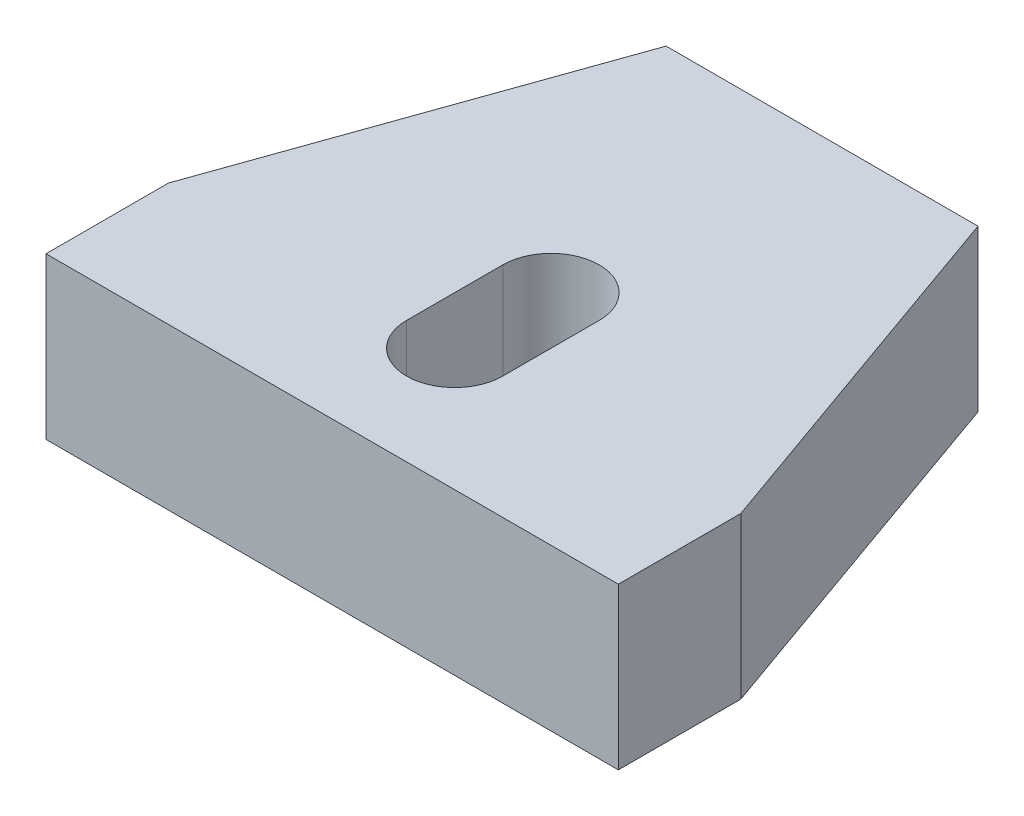
SolidWorks part; units mm, degrees
ref_plane "Front Plane" through (0, 0, 0) normal (0, 0, 1) x (1, 0, 0)
ref_plane "Top Plane" through (0, 0, 0) normal (0, 1, 0) x (1, 0, 0)
ref_plane "Right Plane" through (0, 0, 0) normal (1, 0, 0) x (0, 0, -1)
sketch "Sketch1" plane through (0, 0, 0) normal (0, 1, 0) x (1, 0, 0)
  line L0 (-8.9027, 0) -> (8.9027, 0)
  line L1 (8.9027, 0) -> (8.9027, 3.81)
  line L2 (-8.9027, 0) -> (-8.9027, 3.81)
  line L3 (-4.8514, 15.24) -> (4.8514, 15.24)
  line L4 (8.9027, 3.81) -> (4.8514, 15.24)
  line L5 (-4.8514, 15.24) -> (-8.9027, 3.81)
  line L6 (0, 15.24) -> (0, 0) construction
  line L7 (0, 3.81) -> (0, 6.8072) construction
  line L8 (-1.4986, 3.81) -> (-1.4986, 6.8072)
  line L9 (1.4986, 3.81) -> (1.4986, 6.8072)
  arc A0 (-1.4986, 3.81) -> (1.4986, 3.81) centre (0, 3.81) ccw
  arc A1 (1.4986, 6.8072) -> (-1.4986, 6.8072) centre (0, 6.8072) ccw
  point P4 (0, 0)
  point P10 (0, 15.24)
  point P14 (0, 5.3086)
  dimension "D5" = 3.81
  dimension "D1" = 17.8054
  dimension "D2" = 3.81
  dimension "D3" = 3.81
  dimension "D4" = 9.7028
  dimension "D6" = 15.24
extrude "Boss-Extrude1" add sketch "Sketch1" along normal blind 5.0038
ref_point "Point1"
